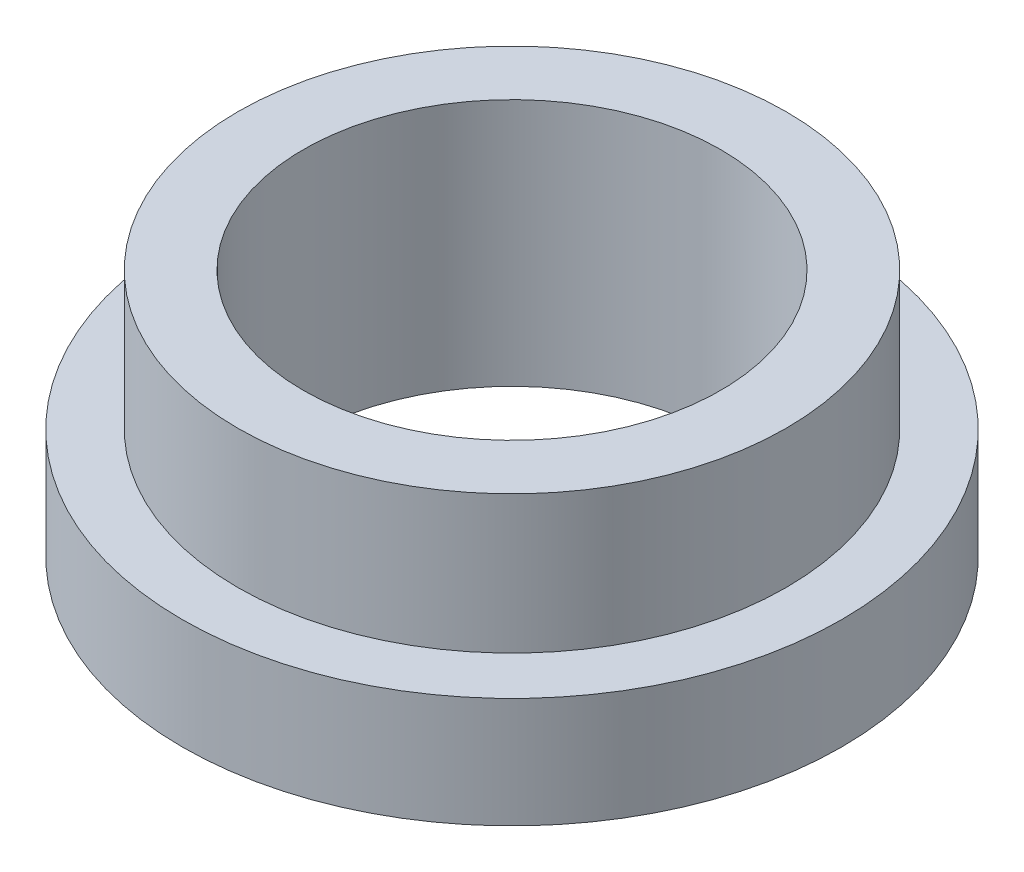
SolidWorks part; units mm, degrees
material "Tin Bearing Bronze"
ref_plane "Front Plane" through (0, 0, 0) normal (0, 0, 1) x (1, 0, 0)
ref_plane "Top Plane" through (0, 0, 0) normal (0, 1, 0) x (1, 0, 0)
ref_plane "Right Plane" through (0, 0, 0) normal (1, 0, 0) x (0, 0, -1)
sketch "Sketch1" plane through (0, 0, 0) normal (0, 0, 1) x (1, 0, 0)
  line L0 (-3.025, 0) -> (-3.025, 3.6)
  line L1 (-3.025, 3.6) -> (-3.975, 3.6)
  line L2 (-3.975, 3.6) -> (-3.975, 1.6)
  line L3 (-3.975, 1.6) -> (-4.78, 1.6)
  line L4 (-4.78, 1.6) -> (-4.78, 0)
  line L5 (-4.78, 0) -> (-3.025, 0)
  line L6 (0, 0) -> (0, 30.0257) construction
  dimension "D1" = 6.05
  dimension "D2" = 9.56
  dimension "D3" = 1.6
  dimension "D4" = 2
  dimension "D5" = 7.95
revolve "Revolve1" add sketch "Sketch1" angle 360 about L6
